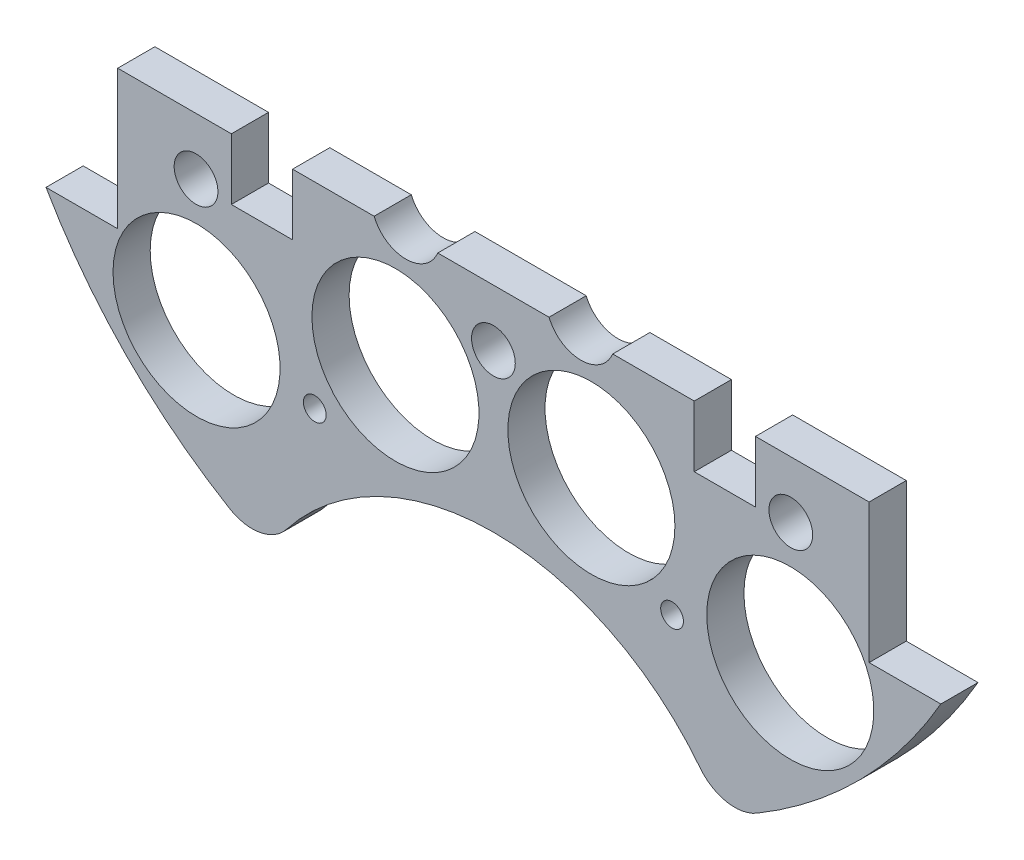
SolidWorks part; units mm, degrees
ref_plane "Front Plane" through (0, 0, 0) normal (0, 0, 1) x (1, 0, 0)
ref_plane "Top Plane" through (0, 0, 0) normal (0, 1, 0) x (1, 0, 0)
ref_plane "Right Plane" through (0, 0, 0) normal (1, 0, 0) x (0, 0, -1)
sketch "Sketch1" plane through (0, 0, 0) normal (0, 0, 1) x (1, 0, 0)
  line L0 (0, 0) -> (-82.1241, 0) construction
  line L1 (0, 0) -> (0, 95.6219) construction
  line L3 (-64.9644, 37.338) -> (-54.5504, 37.338)
  line L5 (-64.9644, -37.338) -> (-54.5504, -37.338)
  line L6 (-54.5504, 37.338) -> (-54.5504, -37.338)
  line L7 (64.9644, -37.338) -> (54.5504, -37.338)
  line L8 (64.9644, 37.338) -> (54.5504, 37.338)
  line L9 (54.5504, 37.338) -> (54.5504, -37.338)
  arc A0 (-64.9644, -37.338) -> (64.9644, -37.338) centre (0, 0) ccw
  circle A1 centre (-46.482, 11.049) radius 1.651
  circle A2 centre (-21.0833, 10.795) radius 1.651
  circle A3 centre (-21.0833, -10.795) radius 1.651
  circle A4 centre (-46.482, -11.049) radius 1.651
  circle A5 centre (46.482, -11.049) radius 1.651
  circle A6 centre (21.0833, -10.795) radius 1.651
  circle A7 centre (21.0833, 10.795) radius 1.651
  circle A8 centre (46.482, 11.049) radius 1.651
  arc A9 (64.9644, 37.338) -> (-64.9644, 37.338) centre (0, 0) ccw
  dimension "D2" = 3.302
  dimension "D3" = 3.302
  dimension "D4" = 25.4
  dimension "D5" = 10.795
  dimension "D10" = 46.482
  dimension "D6" = 74.676
  dimension "D7" = 10.414
  dimension "D8" = 74.93
  dimension "D9" = 74.93
  dimension "D11" = 37.338
extrude "Boss-Extrude2" add sketch "Sketch1" along normal blind 5.3975
sketch "Sketch2" plane through (0, 0, 5.3975) normal (0, 0, 1) x (1, 0, 0)
  line L0 (0, 68.58) -> (0, 55.88) construction
  line L1 (-9.525, 68.58) -> (9.525, 68.58)
  line L2 (-9.525, 68.58) -> (-9.525, 55.88)
  line L3 (-9.525, 55.88) -> (9.525, 55.88)
  line L4 (9.525, 68.58) -> (9.525, 55.88)
  line L5 (-9.525, 62.23) -> (9.525, 62.23) construction
  arc A0 (64.9644, 37.338) -> (-64.9644, 37.338) centre (0, 0) ccw construction
  circle A1 centre (-21.0833, 10.795) radius 1.651 construction
  circle A2 centre (21.0833, 10.795) radius 1.651 construction
  circle A3 centre (-6.731, 62.23) radius 1.143
  circle A4 centre (6.731, 62.23) radius 1.143
  dimension "D4" = 2.286
  dimension "D5" = 0
  dimension "D6" = 6.731
  dimension "D1" = 19.05
  dimension "D2" = 12.7
  dimension "D3" = 55.88
extrude "Cut-Extrude1" cut sketch "Sketch2" against normal through all contours A3 | A4
sketch "Sketch3" plane through (0, 0, 0) normal (0, 0, -1) x (-1, 0, 0)
  line L0 (0, 0) -> (0, -116.2908) construction
  line L1 (0, 0) -> (-153.8039, 0) construction
  line L2 (0, 0) -> (15.2681, -56.9814) construction
  circle A4 centre (-43.1052, -43.1052) radius 12.1285
  circle A6 centre (14.224, -34.29) radius 12.1285
  circle A7 centre (14.224, 34.29) radius 12.1285
  circle A8 centre (-43.1052, 43.1052) radius 12.1285
  circle A11 centre (43.1052, 43.1052) radius 12.1285
  circle A12 centre (-14.224, 34.29) radius 12.1285
  circle A13 centre (-14.224, -34.29) radius 12.1285
  circle A14 centre (43.1052, -43.1052) radius 12.1285
  point P36 (0, 0)
  point P53 (0, 0)
  point P55 (0, 0)
  dimension "D1" = 14.224
  dimension "D2" = 34.29
  dimension "D4" = 15
  dimension "D8" = 24.257
extrude "Cut-Extrude2" cut sketch "Sketch3" against normal through all
sketch "Sketch4" plane through (0, 0, 0) normal (0, 0, -1) x (-1, 0, 0)
  line L1 (-15.7702, 56.3138) -> (12.7925, 56.3138)
  line L2 (-15.7702, 56.3138) -> (-15.7702, 67.9913)
  line L3 (-15.7702, 67.9913) -> (12.7925, 67.9913)
  line L4 (12.7925, 56.3138) -> (12.7925, 67.9913)
extrude "Boss-Extrude3" add sketch "Sketch4" against normal up to surface (5.3975 mm away) up to face at (-55.2337, -43.1052, 5.3975)
sketch "Sketch5" plane through (0, 0, 0) normal (0, 0, -1) x (-1, 0, 0)
  line L1 (-85.044, -17.145) -> (131.6774, -17.145)
  line L2 (-85.044, -17.145) -> (-85.044, 113.4242)
  line L3 (-85.044, 113.4242) -> (131.6774, 113.4242)
  line L4 (131.6774, -17.145) -> (131.6774, 113.4242)
  circle A0 centre (-21.0833, -10.795) radius 1.651 construction
  dimension "D1" = 6.35
extrude "Cut-Extrude4" cut sketch "Sketch5" against normal through all contours L2 L3 L4 L1
sketch "Sketch6" plane through (0, 0, 0) normal (0, 0, -1) x (-1, 0, 0)
  line L0 (-33.02, -67.2621) -> (33.02, -67.2621)
  line L1 (0, 0) -> (0, -146.3858) construction
  arc A0 (-64.9644, -37.338) -> (64.9644, -37.338) centre (0, 0) ccw construction
  circle A1 centre (0, -86.3121) radius 38.1
  dimension "D2" = 76.2
  dimension "D1" = 66.04
  dimension "D3" = 19.05
extrude "Cut-Extrude5" cut sketch "Sketch6" against normal blind 60.96 contours A1
extrude "Cut-Extrude6" cut sketch "Sketch7" against normal through all both and the other way through all
sketch "Sketch7" plane through (-31.3134, 132.614, 31.75) normal (0, 0, 1) x (0, 1, 0)
  line L0 (-132.614, -31.3134) -> (-132.614, 57.8454) construction
  line L1 (-132.614, -31.3134) -> (-222.516, -31.3134) construction
  circle A0 centre (-158.014, 14.4066) radius 3.175
  circle A1 centre (-173.254, -31.3134) radius 3.175
  circle A3 centre (-158.014, -77.0334) radius 3.175
  circle A4 centre (-107.214, -77.0334) radius 3.175
  circle A5 centre (-91.974, -31.3134) radius 3.175
  circle A6 centre (-107.214, 14.4066) radius 3.175
fillet "Fillet1" radius 6.35 1 edges at (-33.001, -67.2714, 2.6987)
fillet "Fillet2" radius 6.35 1 edges at (33.001, -67.2714, 2.6987)
extrude "Cut-Extrude8" cut sketch "Sketch9" against normal blind 29.21
sketch "Sketch9" plane through (-31.3134, 132.559, 28.575) normal (0, 0, 1) x (0, 1, 0)
  line L0 (-132.559, -31.3134) -> (6.1626, -31.3134) construction
  line L2 (-132.559, -31.3134) -> (-132.559, -122.6589) construction
  circle A0 centre (-190.979, 2.9766) radius 1.651
  circle A2 centre (-154.784, -31.3134) radius 1.651
  circle A3 centre (-190.979, -65.6034) radius 1.651
  circle A4 centre (-110.334, -31.3134) radius 1.651
  circle A5 centre (-74.139, -65.6034) radius 1.651
  circle A6 centre (-74.139, 2.9766) radius 1.651
extrude "Cut-Extrude99" cut sketch "Sketch100" against normal blind 29.21
sketch "Sketch100" plane through (-31.3134, 132.559, 22.225) normal (0, 0, 1) x (0, 1, 0)
  line L0 (-143.7712, -34.3645) -> (6.1626, -34.3645) construction
  line L2 (-143.7712, -34.3645) -> (-143.7712, -122.6589) construction
  circle A0 centre (-202.1912, -0.0745) radius 1.651
  circle A2 centre (-165.9962, -34.3645) radius 1.651
  circle A3 centre (-202.1912, -68.6545) radius 1.651
  circle A4 centre (-121.5462, -34.3645) radius 1.651
  circle A5 centre (-85.3512, -68.6545) radius 1.651
  circle A6 centre (-85.3512, -0.0745) radius 1.651
sketch "Sketch102" plane through (0, 0, 0) normal (0, 0, -1) x (-1, 0, 0)
  line L0 (-54.5504, -17.145) -> (54.5504, -17.145) construction
  line L1 (-38.0504, -17.145) -> (-29.1604, -17.145)
  line L2 (-38.0504, -17.145) -> (-38.0504, -26.035)
  line L3 (-38.0504, -26.035) -> (-29.1604, -26.035)
  line L4 (-29.1604, -17.145) -> (-29.1604, -26.035)
  line L5 (0, 15.7454) -> (0, -80.7771) construction
  line L6 (29.1604, -17.145) -> (38.0504, -17.145)
  line L7 (29.1604, -17.145) -> (29.1604, -26.035)
  line L8 (29.1604, -26.035) -> (38.0504, -26.035)
  line L9 (38.0504, -17.145) -> (38.0504, -26.035)
  line L10 (-54.5504, -37.338) -> (-54.5504, -17.145) construction
  dimension "D1" = 8.89
  dimension "D2" = 8.89
  dimension "D3" = 16.5
extrude "Cut-Extrude101" cut sketch "Sketch102" against normal through all
sketch "Sketch105" plane through (0, 0, 0) normal (0, 0, -1) x (-1, 0, 0)
  line L0 (0, 0) -> (0, -99.3188) construction
  circle A0 centre (-12.7, -15.24) radius 5
  circle A1 centre (12.7, -15.24) radius 5
  dimension "D1" = 10
  dimension "D2" = 12.7
  dimension "D3" = 15.24
extrude "Cut-Extrude104" cut sketch "Sketch105" against normal blind 10
extrude "Cut-Extrude105" cut sketch "Sketch106" against normal through all and the other way blind 103.378
sketch "Sketch106" plane through (30.092, 4.0835, 22.2885) normal (0, 0, -1) x (-1, 0, 0)
  line L0 (30.092, -4.0835) -> (148.6336, -4.0835) construction
  line L1 (30.092, -4.0835) -> (30.092, 90.452) construction
  circle A0 centre (-13.088, 21.3165) radius 3.175
  circle A1 centre (73.272, 21.3165) radius 3.175
  circle A2 centre (30.092, 21.3165) radius 3.175
  circle A4 centre (73.272, -29.4835) radius 3.175
  circle A5 centre (30.092, -29.4835) radius 3.175
  circle A6 centre (-13.088, -29.4835) radius 3.175
extrude "Cut-Extrude157" cut sketch "Sketch158" against normal blind 97.79
sketch "Sketch158" plane through (30.092, 4.0835, -24.638) normal (0, 0, -1) x (-1, 0, 0)
  line L0 (30.092, -29.4835) -> (30.092, 6.2385) construction
  circle A0 centre (4.1544, -49.7288) radius 1.651
  circle A4 centre (56.0296, -49.7288) radius 1.651
  circle A5 centre (4.1544, 41.3825) radius 1.651
  circle A9 centre (56.0296, 41.3825) radius 1.651
